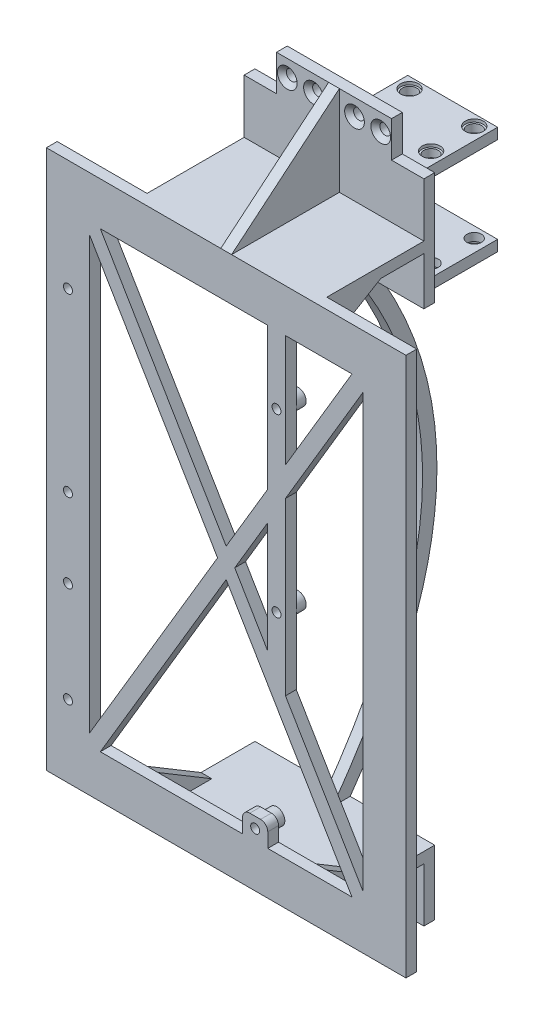
SolidWorks part; units mm, degrees
ref_plane "Front Plane" through (0, 0, 0) normal (0, 0, 1) x (1, 0, 0)
ref_plane "Top Plane" through (0, 0, 0) normal (0, 1, 0) x (1, 0, 0)
ref_plane "Right Plane" through (0, 0, 0) normal (1, 0, 0) x (0, 0, -1)
sketch "Sketch1" plane through (0, 0, 0) normal (0, 0, 1) x (1, 0, 0)
  line L0 (-64.6356, 0) -> (-2.3902, 0) construction
  line L1 (-50, 75) -> (50, 75)
  line L2 (-50, 75) -> (-50, -75)
  line L3 (-50, -75) -> (50, -75)
  line L4 (50, 75) -> (50, -75)
  line L5 (-50, 75) -> (50, -75) construction
  line L6 (-50, -75) -> (50, 75) construction
  line L7 (0, 67.0859) -> (0, 4.0274) construction
  line L8 (-35, 63) -> (35, 63)
  line L9 (38, 60) -> (38, -60)
  line L10 (-35, -63) -> (35, -63)
  line L11 (-38, 60) -> (-38, -60)
  line L12 (-35, 63) -> (0, 4.0274)
  line L13 (35, -63) -> (0, -4.0274)
  line L14 (35, 63) -> (0, 4.0274)
  line L15 (-35, -63) -> (0, -4.0274)
  line L16 (-38, 63) -> (38, 63) construction
  line L17 (-38, 63) -> (-38, -63) construction
  line L18 (-38, 70.1739) -> (-38, 80.5438) construction
  line L19 (-29.6469, 63) -> (-38, 63) construction
  line L20 (38, 63) -> (38, -63) construction
  line L21 (-38, -63) -> (38, -63) construction
  line L22 (-2.3902, 0) -> (-38, -60)
  line L23 (0, -4.0274) -> (0, -100.9095) construction
  line L24 (2.3902, 0) -> (38, -60)
  line L25 (-2.3902, 0) -> (-38, 60)
  line L26 (2.3902, 0) -> (38, 60)
  line L27 (2.3902, 0) -> (62.7019, 0) construction
  point P0 (0, 0)
  point P6 (0, -63)
  point P7 (0, -75)
  point P18 (-35, 63)
  point P19 (-38, 60)
  point P20 (38, 60)
  point P21 (35, 63)
  point P22 (38, -60)
  point P23 (35, -63)
  point P24 (-35, -63)
  point P25 (-38, -60)
  dimension "D1" = 150
  dimension "D2" = 100
  dimension "D3" = 12
  dimension "D5" = 3
  dimension "D6" = 3
extrude "Boss-Extrude1" add sketch "Sketch1" along normal blind 3
sketch "Sketch2" plane through (0, 0, 0) normal (0, 0, -1) x (-1, 0, 0)
  line L0 (-50, 75) -> (50, 75) construction
  line L1 (-25, 75) -> (25, 75)
  line L2 (-25, 75) -> (-25, 72)
  line L3 (-25, 72) -> (25, 72)
  line L4 (25, 75) -> (25, 72)
  dimension "D1" = 25
  dimension "D2" = 25
  dimension "D3" = 3
extrude "Boss-Extrude2" add sketch "Sketch2" along normal blind 30
sketch "Sketch3" plane through (0, 75, 0) normal (0, 1, 0) x (1, 0, 0)
  line L0 (25, 30) -> (25, 0) construction
  line L1 (-25, 30) -> (25, 30)
  line L2 (-25, 30) -> (-25, 27)
  line L3 (-25, 27) -> (25, 27)
  line L4 (25, 30) -> (25, 27)
  dimension "D1" = 3
extrude "Boss-Extrude3" add sketch "Sketch3" along normal blind 25
sketch "Sketch6" plane through (0, 0, -30) normal (0, 0, -1) x (-1, 0, 0)
  line L0 (-27.9147, 95.34) -> (25, 95.34) construction
  line L1 (25, 95.34) -> (25, 100) construction
  line L3 (0, 100) -> (0, 72) construction
  line L4 (-25, 100) -> (25, 100) construction
  line L5 (-25, 72) -> (25, 72) construction
  point P6 (5.7, 95.34)
  point P7 (13, 95.34)
  dimension "D1" = 12
  dimension "D2" = 7.3
  dimension "D3" = 4.66
hole_wizard "Ø3.0mm Dowel Hole1" positions "Sketch8" profile "Sketch7" hole size "Ø3.0" standard "DIN"
sketch "Sketch8" plane through (0, 0, -30) normal (0, 0, -1) x (-1, 0, 0)
  point P0 (13, 95.34)
  point P3 (5.7, 95.34)
sketch "Sketch7" plane through (-13, 95.34, -30) normal (1, 0, 0) x (0, 1, 0)
  line L0 (0, 0) -> (0, 10.9013)
  line L1 (0, 10.9013) -> (1.5, 10)
  line L2 (1.5, 10) -> (1.5, 0)
  line L5 (1.5, 0) -> (0, 0)
  line L10 (0, 10.9013) -> (-1.5, 10) construction
  line L11 (0, -6.35) -> (0, 107.95) construction
  dimension "Hole Dia." = 3
  dimension "Hole Depth" = 10
  dimension "Drill Angle" = 118
sketch "Sketch37" plane through (0, 0, -27) normal (0, 0, 1) x (1, 0, 0)
  circle A0 centre (-13, 95.34) radius 2.75
  circle A1 centre (-5.7, 95.34) radius 2.75
  dimension "D1" = 5.5
  dimension "D2" = 5.5
extrude "Cut-Extrude2" cut sketch "Sketch37" against normal blind 10 draft 45
sketch "Sketch9" plane through (0, 0, 0) normal (1, 0, 0) x (0, 0, -1)
  line L0 (-3, 75) -> (27, 100)
rib "Rib1" sketch "Sketch9" sketch "Sketch9" thickness 3 extrusion direction parallel to sketch draft on no parameters "D1"=3
ref_plane "Plane2" through (-25, 72, 0) normal (-1, 0, 0) x (0, 0, 1)
ref_point "Point1"
sketch "Sketch11" plane through (-25, 72, 0) normal (-1, 0, 0) x (0, 0, 1)
  line L0 (-15, 0) -> (0, -9)
  line L1 (-30, 0) -> (0, 0) construction
rib "Rib5" sketch "Sketch11" sketch "Sketch11" thickness 3 extrusion direction parallel to sketch draft on no parameters "D1"=3
mirror "Mirror1" about plane through (0, 0, 0) normal (1, 0, 0) of "Cut-Extrude2", "Ø3.0mm Dowel Hole1", "Rib5"
mirror "Mirror2" about plane through (0, 0, 0) normal (0, 1, 0) of "Mirror1", "Rib5", "Rib1", "Ø3.0mm Dowel Hole1", "Boss-Extrude2", "Boss-Extrude3", "Cut-Extrude2"
ref_point "Point2"
sketch "Sketch14" plane through (0, 72, 0) normal (0, -1, 0) x (1, 0, 0)
  line L0 (25, -30) -> (25, -15) construction
  line L1 (-25, -30) -> (25, -30)
  line L2 (-25, -30) -> (-25, -27)
  line L3 (-25, -27) -> (25, -27)
  line L4 (25, -30) -> (25, -27)
  dimension "D1" = 3
extrude "Boss-Extrude5" add sketch "Sketch14" along normal blind 13.32
sketch "Sketch15" plane through (0, 0, -30) normal (0, 0, -1) x (-1, 0, 0)
  line L0 (25, 58.68) -> (-25, 58.68) construction
  line L1 (3.5, 58.68) -> (-21.5, 58.68)
  line L2 (3.5, 58.68) -> (3.5, 61.68)
  line L3 (3.5, 61.68) -> (-21.5, 61.68)
  line L4 (-21.5, 58.68) -> (-21.5, 61.68)
  line L5 (3.5, 100) -> (3.5, 58.68) construction
  line L6 (-25, 100) -> (25, 100) construction
  line L8 (3.5, 85.68) -> (-21.5, 85.68)
  line L9 (3.5, 85.68) -> (3.5, 88.68)
  line L10 (3.5, 88.68) -> (-21.5, 88.68)
  line L11 (-21.5, 85.68) -> (-21.5, 88.68)
  dimension "D1" = 3
  dimension "D2" = 3.5
  dimension "D3" = 25
  dimension "D4" = 3
  dimension "D5" = 25
  dimension "D6" = 24
extrude "Boss-Extrude6" add sketch "Sketch15" along normal blind 21
ref_point "Point3"
sketch "Sketch13" plane through (0, 0, 0) normal (1, 0, 0) x (0, 0, -1)
  line L0 (0, 0) -> (65.8388, 0) construction
  line L1 (27, 58.68) -> (32, 58.68)
  line L2 (30, -72) -> (23.4251, -72) construction
  line L3 (30, -72) -> (25, -72)
  spline S0 degree 2 poles (27, 58.68) (74.2435, -5.7106) (25, -72) knots 0 0 0 1 1 1
  spline S1 degree 2 poles (32, 58.68) (77.2303, -5.8059) (30, -72) knots 0 0 0 1 1 1
  dimension "D1" = 5
  dimension "D2" = 50
  dimension "D3" = 4
  dimension "D4" = 5
extrude "Boss-Extrude7" add sketch "Sketch13" along normal blind 1.5 and the other way blind 1.5
sketch "Sketch17" plane through (0, 88.68, 0) normal (0, 1, 0) x (1, 0, 0)
  line L0 (0, 51) -> (0, 30) construction
  line L1 (-3.5, 51) -> (21.5, 51) construction
  line L2 (-3.5, 30) -> (21.5, 30) construction
  line L4 (9, 51) -> (9, 30) construction
  point P9 (0, 48)
  point P10 (0, 36)
  point P11 (18, 36)
  point P12 (18, 48)
  dimension "D1" = 3.5
  dimension "D2" = 9
  dimension "D3" = 6
  dimension "D4" = 12
hole_wizard "CBORE for M5 Hex Head Bolt1" positions "Sketch19" profile "Sketch20" counterbore size "M5" standard "ANSI Metric"
sketch "Sketch19" plane through (0, 88.68, 0) normal (0, 1, 0) x (1, 0, 0)
  point P0 (0, 48)
  point P3 (0, 36)
  point P6 (18, 48)
  point P9 (18, 36)
sketch "Sketch20" plane through (0, 88.68, -48) normal (1, 0, 0) x (0, 0, 1)
  line L0 (0, 0) -> (0, 11.1781)
  line L1 (0, 11.1781) -> (2, 10)
  line L2 (2, 10) -> (2, 0.8)
  line L3 (2, 0.8) -> (2.5, 0.8)
  line L4 (2.5, 0.8) -> (2.5, 0)
  line L5 (2.5, 0) -> (0, 0)
  line L10 (0, 11.1781) -> (-2, 10) construction
  line L11 (0, -6.35) -> (0, 107.95) construction
  dimension "Hole Dia." = 4
  dimension "Hole Depth" = 10
  dimension "C'Bore Dia." = 5
  dimension "C'Bore Depth" = 0.8
  dimension "Drill Angle" = 119
ref_plane "Plane3" through (0, 73.68, 0) normal (0, 1, 0) x (1, 0, 0)
mirror "Mirror3" about plane through (0, 73.68, 0) normal (0, 1, 0) of "CBORE for M5 Hex Head Bolt1"
sketch "Sketch21" plane through (0, 0, -30) normal (0, 0, -1) x (-1, 0, 0)
  line L0 (-16, 100) -> (-16, 90)
  line L1 (-25, 100) -> (25, 100) construction
  line L2 (-16, 90) -> (-25, 90)
  line L3 (-25, 100) -> (-25, 58.68) construction
  line L4 (-25, 90) -> (-25, 100)
  line L5 (-25, 100) -> (-16, 100)
  line L6 (-27.9147, 95.34) -> (25, 95.34) construction
  point P4 (-16, 95.34)
  point P11 (-13, 95.34)
  dimension "D1" = 3
  dimension "D2" = 10
extrude "Cut-Extrude1" cut sketch "Sketch21" against normal blind 3
mirror "Mirror4" about plane through (0, 0, 0) normal (1, 0, 0) of "Cut-Extrude1"
mirror "Mirror5" about plane through (0, 0, 0) normal (0, 1, 0) of "Cut-Extrude1", "Mirror4"
sketch "Sketch22" plane through (0, 0, 0) normal (0, 0, -1) x (-1, 0, 0)
  line L0 (32.6598, -63) -> (52.5656, -63) construction
  line L1 (35, -63) -> (25, -63) construction
  line L4 (44, -63) -> (44, 79.4754) construction
  line L5 (50, 75) -> (50, -75) construction
  line L6 (50, -40.91) -> (38, -40.91) construction
  line L7 (38, 60) -> (38, -60) construction
  circle A0 centre (44, -54.88) radius 2.25
  circle A1 centre (44, -26.94) radius 2.25
  circle A2 centre (44, -4.94) radius 2.25
  circle A3 centre (44, 44.06) radius 2.25
  point P4 (44, -54.88)
  dimension "D3" = 4.5
  dimension "D5" = 4.5
  dimension "D6" = 4.5
  dimension "D1" = 8.12
  dimension "D2" = 6
  dimension "D4" = 13.97
  dimension "D7" = 22
  dimension "D8" = 49
extrude "Boss-Extrude8" add sketch "Sketch22" along normal blind 3
hole_wizard "Ø2.5mm Dowel Hole2" positions "Sketch24" profile "Sketch25" hole size "Ø2.5" standard "ANSI Metric"
sketch "Sketch24" plane through (0, 0, -3) normal (0, 0, -1) x (-1, 0, 0)
  point P0 (44, -54.88)
sketch "Sketch25" plane through (-44, -54.88, -3) normal (1, 0, 0) x (0, 1, 0)
  line L0 (0, 0) -> (0, 10.7511)
  line L1 (0, 10.7511) -> (1.25, 10)
  line L2 (1.25, 10) -> (1.25, 0)
  line L5 (1.25, 0) -> (0, 0)
  line L10 (0, 10.7511) -> (-1.25, 10) construction
  line L11 (0, -6.35) -> (0, 107.95) construction
  dimension "Hole Dia." = 2.5
  dimension "Hole Depth" = 10
  dimension "Drill Angle" = 118
sketch "Sketch30" plane through (0, 0, -3) normal (0, 0, -1) x (-1, 0, 0)
  point P0 (44, -26.94)
  point P1 (44, -26.94)
  point P3 (44, -4.94)
  point P4 (44, 44.06)
hole_wizard "Ø2.5mm Dowel Hole1" positions "Sketch32" profile "Sketch31" hole size "Ø2.5" standard "DIN"
sketch "Sketch32" plane through (0, 0, -3) normal (0, 0, -1) x (-1, 0, 0)
  point P0 (44, -26.94)
  point P3 (44, -4.94)
  point P6 (44, 44.06)
sketch "Sketch31" plane through (-44, -26.94, -3) normal (1, 0, 0) x (0, 1, 0)
  line L0 (0, 0) -> (0, 10.7511)
  line L1 (0, 10.7511) -> (1.25, 10)
  line L2 (1.25, 10) -> (1.25, 0)
  line L5 (1.25, 0) -> (0, 0)
  line L10 (0, 10.7511) -> (-1.25, 10) construction
  line L11 (0, -6.35) -> (0, 107.95) construction
  dimension "Hole Dia." = 2.5
  dimension "Hole Depth" = 10
  dimension "Drill Angle" = 118
sketch "Sketch33" plane through (0, 0, 0) normal (0, 0, 1) x (1, 0, 0)
  line L0 (-22, -63) -> (22, -63) construction
  line L1 (11.57, -63) -> (4.57, -63)
  line L2 (11.57, -63) -> (11.57, -57)
  line L3 (11.57, -57) -> (4.57, -57)
  line L4 (4.57, -63) -> (4.57, -57)
  circle A0 centre (8.07, -59.96) radius 1.25
  circle A7 centre (8.07, -59.96) radius 1.5875 construction
  point P0 (8.07, -59.96)
  dimension "D3" = 2.5
  dimension "D1" = 3.5
  dimension "D2" = 7
  dimension "D4" = 6
extrude "Boss-Extrude9" add sketch "Sketch33" along normal blind 3
sketch "Sketch34" plane through (0, 0, 0) normal (0, 0, -1) x (-1, 0, 0)
  circle A0 centre (-8.07, -59.96) radius 2.25
  circle A2 centre (-8.07, -59.96) radius 1.25
  circle M9 centre (-8.07, -59.96) radius 1.25
  dimension "D1" = 4.5
  dimension "D2" = 2.5
extrude "Boss-Extrude10" add sketch "Sketch34" along normal blind 3 contours A0 M9
fillet "Fillet1" radius 2 1 edges at (11.57, -57, 1.5)
fillet "Fillet2" radius 2 1 edges at (4.57, -57, 1.5)
sketch "Sketch35" plane through (0, 0, 0) normal (0, 0, -1) x (-1, 0, 0)
  line L0 (-11.5, 63) -> (-11.5, -15.3493)
  line L1 (-22, 63) -> (22, 63) construction
  line L2 (-2.3902, 0) -> (-38, -60) construction
  line L3 (-16.5, 63) -> (-16.5, -23.774)
  line L4 (-11.5, 36.814) -> (-16.5, 36.814) construction
  line L5 (-14, -19.5616) -> (-14, 63) construction
  line L6 (44, -4.94) -> (-14, -4.94) construction
  line L7 (44, 44.06) -> (-14, 44.06) construction
  line L8 (-11.5, 63) -> (-16.5, 63)
  line L9 (-11.5, -15.3493) -> (-16.5, -23.774)
  line L10 (-16.5, -23.774) -> (-16.4011, -23.5939)
  circle A0 centre (-14, 44.06) radius 1.25
  circle A1 centre (-14, -4.94) radius 1.25
  point P12 (-14, 36.814)
  line M21 (0, 4.0274) -> (-35, 63)
  line M27 (-2.3902, 0) -> (-38, -60)
  line M29 (-38, 60) -> (-2.3902, 0)
  dimension "D3" = 2.5
  dimension "D4" = 2.5
  dimension "D1" = 5
  dimension "D2" = 58
extrude "Boss-Extrude11" add sketch "Sketch35" against normal blind 3 contours L3 L0 A1 M29 M27 | L0 L8 L3 A0 M21
sketch "Sketch36" plane through (0, 0, 0) normal (0, 0, -1) x (-1, 0, 0)
  circle A0 centre (-14, 44.06) radius 1.25
  circle A1 centre (-14, 44.06) radius 2.25
  circle A2 centre (-14, -4.94) radius 1.25
  circle A3 centre (-14, -4.94) radius 2.25
  dimension "D1" = 4.5
  dimension "D2" = 4.5
extrude "Boss-Extrude12" add sketch "Sketch36" along normal blind 3
